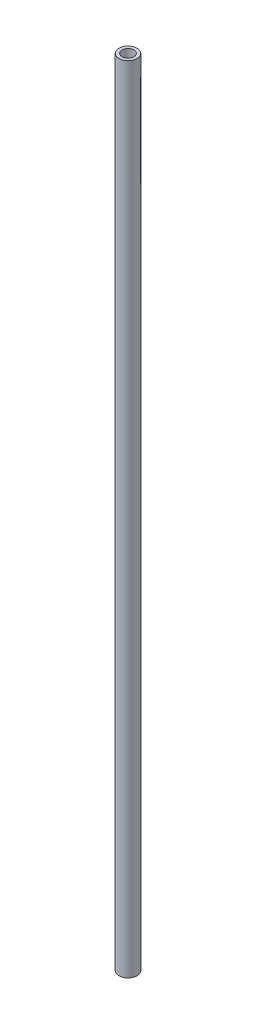
SolidWorks part; units mm, degrees
ref_plane "Front Plane" through (0, 0, 0) normal (0, 0, 1) x (1, 0, 0)
ref_plane "Top Plane" through (0, 0, 0) normal (0, 1, 0) x (1, 0, 0)
ref_plane "Right Plane" through (0, 0, 0) normal (1, 0, 0) x (0, 0, -1)
sketch "Sketch1" plane through (0, 0, 0) normal (0, 1, 0) x (1, 0, 0)
  circle A0 centre (0, 0) radius 2.9
  circle A1 centre (0, 0) radius 1.9
  dimension "D1" = 5.8
  dimension "D2" = 1
extrude "Boss-Extrude1" add sketch "Sketch1" along normal blind 255.3116
